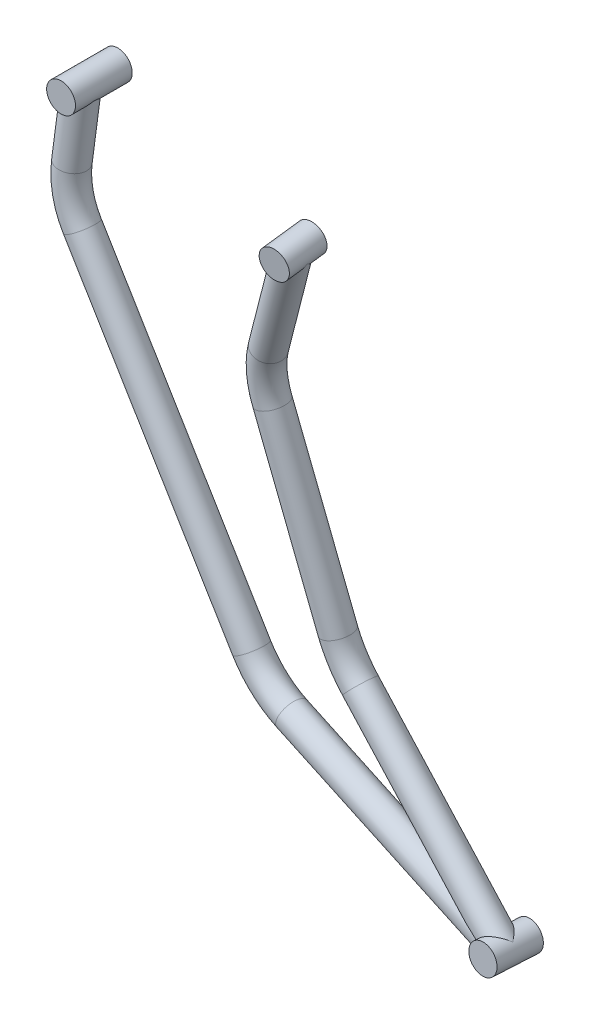
SolidWorks part; units mm, degrees
ref_plane "Front" through (0, 0, 0) normal (0, 0, 1) x (1, 0, 0)
ref_plane "Top" through (0, 0, 0) normal (0, 1, 0) x (1, 0, 0)
ref_plane "Right" through (0, 0, 0) normal (1, 0, 0) x (0, 0, -1)
sketch3d "3DSketch1"
  line L0 (159.0887, -490.6063, 40.4975) -> (21.7937, -364.3365, 28.7184)
  line L1 (162.7964, -496.4435, -134.3658) -> (159.18, -490.7501, 36.1908) construction
  line L2 (7.5128, -351.2024, -142.5068) -> (7.5128, -351.2024, 27.4932) construction
  line L3 (1.7966, -332.6561, 28.637) -> (-46.2684, -176.7082, 38.2546)
  line L4 (-53.1655, -154.3307, -150.3653) -> (-53.1655, -154.3307, 39.6347) construction
  line L5 (-9.928, -34.6675, -153.4431) -> (-9.928, -34.6675, 56.5569) construction
  line L6 (-45.2638, -132.4623, 42.7272) -> (-9.928, -34.6675, 56.5569)
  line L7 (159.0887, -490.6063, 40.4975) -> (-47.0551, -424.1752, 20.3766)
  line L8 (-71.4976, -416.2984, 17.9909) -> (-71.4976, -416.2984, -142.0091) construction
  line L9 (-85.1251, -394.4034, 17.7355) -> (-237.0679, -150.2816, 14.8877)
  line L10 (-249.7686, -129.8757, 14.6496) -> (-249.7686, -129.8757, -155.3504) construction
  line L11 (-247.2596, -105.9819, 13.9052) -> (-240.8772, -45.2007, 12.0115)
  line L13 (159.0887, -490.6063, 40.4975) -> (162.7964, -496.4435, -134.3658) construction
  line L14 (-240.8772, -45.2007, 12.0115) -> (-240.8772, -45.2007, -157.9885) construction
  line L15 (-9.928, -34.6675, -153.4431) -> (-240.8772, -45.2007, -157.9885) construction
  line L16 (-240.8772, -45.2007, -157.9885) -> (-249.7686, -129.8757, -155.3504) construction
  line L17 (-249.7686, -129.8757, -155.3504) -> (-71.4976, -416.2984, -142.0091) construction
  line L18 (-71.4976, -416.2984, -142.0091) -> (162.7964, -496.4435, -134.3658) construction
  line L19 (162.7964, -496.4435, -134.3658) -> (7.5128, -351.2024, -142.5068) construction
  line L20 (7.5128, -351.2024, -142.5068) -> (-53.1655, -154.3307, -150.3653) construction
  line L21 (-53.1655, -154.3307, -150.3653) -> (-9.928, -34.6675, -153.4431) construction
  arc A0 (-47.0551, -424.1752, 20.3766) -> (-85.1251, -394.4034, 17.7355) centre (-26.2559, -357.656, 26.9026) ccw
  arc A4 (1.7966, -332.6561, 28.637) -> (21.7937, -364.3365, 28.7184) centre (67.3145, -313.4123, 44.0344) ccw
  arc A5 (-45.2638, -132.4623, 42.7272) -> (-46.2684, -176.7082, 38.2546) centre (20.128, -156.8521, 48.116) ccw
  arc A6 (-237.0679, -150.2816, 14.8877) -> (-247.2596, -105.9819, 13.9052) centre (-177.6672, -113.3411, 12.2492) ccw
  point P15 (0, 0, 0)
  point P17 (0, 0, 0)
  point P18 (0, 0, 0)
  point P19 (0, 0, 0)
  point P22 (-71.4976, -416.2984, 17.9909)
  point P25 (-18.1096, -353.3952, -42.4911)
  point P26 (0, 0, 0)
  point P27 (0, 0, 0)
  point P28 (0, 0, 0)
  point P32 (7.5128, -351.2024, 27.4932)
  point P34 (53.7578, -321.7943, 112.1957)
  point P37 (-53.1655, -154.3307, 39.6347)
  point P39 (11.8886, -163.6581, 117.2954)
  point P42 (-249.7686, -129.8757, 14.6496)
  point P44 (-179.5413, -115.3235, -57.6976)
  dimension "D5" = 70
  dimension "D6" = 70
  dimension "D7" = 70
  dimension "D9" = 175
  dimension "D10" = 170
  dimension "D11" = 70
  dimension "D1" = 190
  dimension "D2" = 210
  dimension "D3" = 160
  dimension "D4" = 170
  dimension "D8" = 170
ref_plane "Plane1" through (-240.8772, -45.2007, 12.0115) normal (0.1044, 0.9941, -0.031) x (0.9945, -0.1046, -0.004)
sketch "Sketch2" plane through (-240.8772, -45.2007, 12.0115) normal (0.1044, 0.9941, -0.031) x (0.9945, -0.1046, -0.004)
  circle A0 centre (0, 0) radius 12.7
  dimension "D1" = 25.4
sweep "Sweep1" add profiles "Sketch2" path "3DSketch1"
sketch3d "3DSketch3"
  line L0 (-240.8772, -45.2007, 12.0115) -> (-240.8772, -45.2007, -19.13) construction
  line L1 (-9.928, -34.6675, 56.5569) -> (-10.7755, -33.3333, 38.8947) construction
  line L2 (159.0887, -490.6063, 40.4975) -> (159.5707, -491.3651, 17.7653) construction
  circle A0 centre (-240.8772, -45.2007, -19.13) radius 6 construction
  circle A2 centre (-10.7755, -33.3333, 38.8947) radius 6 construction
  point P5 (-241.0043, -45.0006, -13.1347)
  point P8 (-240.8772, -45.2007, -19.13)
  point P11 (-10.9026, -33.1332, 44.89)
ref_plane "Plane2" through (-240.8772, -45.2007, -19.13) normal (0, 0, -1) x (-1, 0, 0)
ref_plane "Plane3" through (-10.7755, -33.3333, 38.8947) normal (-0.0478, 0.0752, -0.996) x (-0.9989, -0.0036, 0.0477)
ref_plane "Plane4" through (159.5707, -491.3651, 17.7653) normal (0.0212, -0.0334, -0.9992) x (-0.9998, -0.0007, -0.0212)
sketch "Sketch3" plane through (-240.8772, -45.2007, -19.13) normal (0, 0, -1) x (-1, 0, 0)
  circle A0 centre (-1.0137, 0) radius 12.7
  dimension "D1" = 25.4
extrude "Boss-Extrude1" add sketch "Sketch3" against normal blind 50
sketch "Sketch4" plane through (-10.7755, -33.3333, 38.8947) normal (-0.0478, 0.0752, -0.996) x (-0.9989, -0.0036, 0.0477)
  circle A0 centre (0, 0) radius 12.7
  dimension "D1" = 25.4
extrude "Boss-Extrude2" add sketch "Sketch4" against normal blind 35
sketch "Sketch5" plane through (159.5707, -491.3651, 17.7653) normal (0.0212, -0.0334, -0.9992) x (-0.9998, -0.0007, -0.0212)
  circle A0 centre (0, 0) radius 12.7
  dimension "D1" = 25.4
extrude "Cut-Extrude1" cut sketch "Sketch5" against normal through all
sketch "Sketch6" plane through (159.5707, -491.3651, 17.7653) normal (0.0212, -0.0334, -0.9992) x (-0.9998, -0.0007, -0.0212)
  circle A0 centre (0, 0) radius 12.7
  dimension "D1" = 25.4
extrude "Boss-Extrude3" add sketch "Sketch6" against normal blind 40
